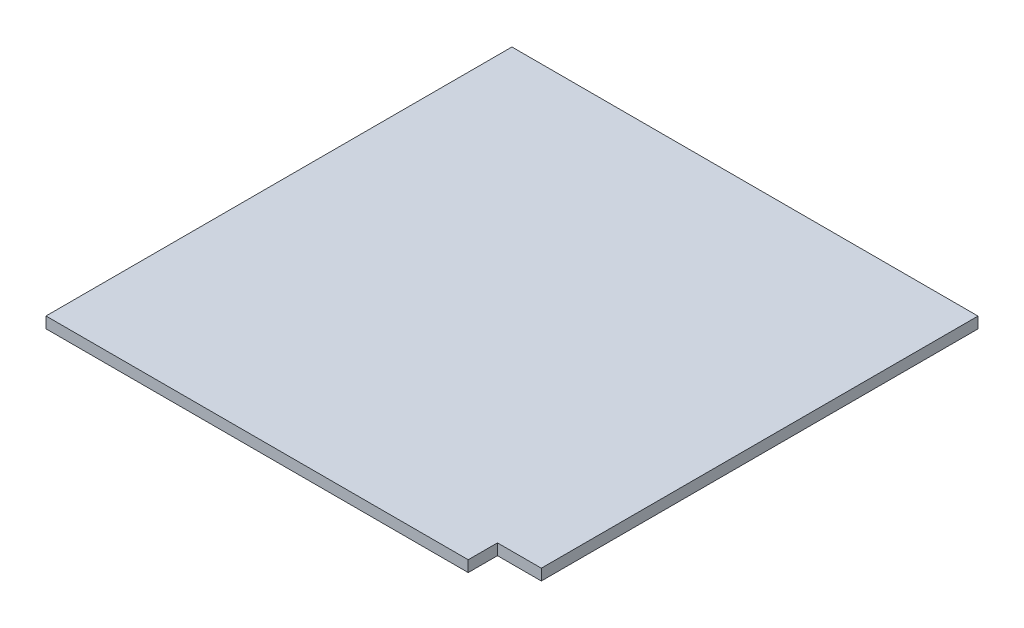
SolidWorks part; units mm, degrees
ref_plane "Front Plane" through (0, 0, 0) normal (0, 0, 1) x (1, 0, 0)
ref_plane "Top Plane" through (0, 0, 0) normal (0, 1, 0) x (1, 0, 0)
ref_plane "Right Plane" through (0, 0, 0) normal (1, 0, 0) x (0, 0, -1)
sketch "Sketch1" plane through (0, 0, 0) normal (0, 1, 0) x (1, 0, 0)
  line L0 (88.815, 0) -> (88.815, 6)
  line L1 (2.185, 0) -> (97.815, 0) construction
  line L2 (2.185, 0) -> (2.185, 95.6)
  line L3 (2.185, 95.6) -> (97.815, 95.6)
  line L4 (97.815, 0) -> (97.815, 95.6) construction
  line L5 (88.815, 6) -> (97.815, 6)
  line L6 (88.815, 0) -> (2.185, 0)
  line L7 (97.815, 6) -> (97.815, 95.6)
extrude "Boss-Extrude1" add sketch "Sketch1" along normal blind 2.286
ref_plane "center-of-slot" through (0, 1.143, 0) normal (0, 1, 0) x (1, 0, 0)
